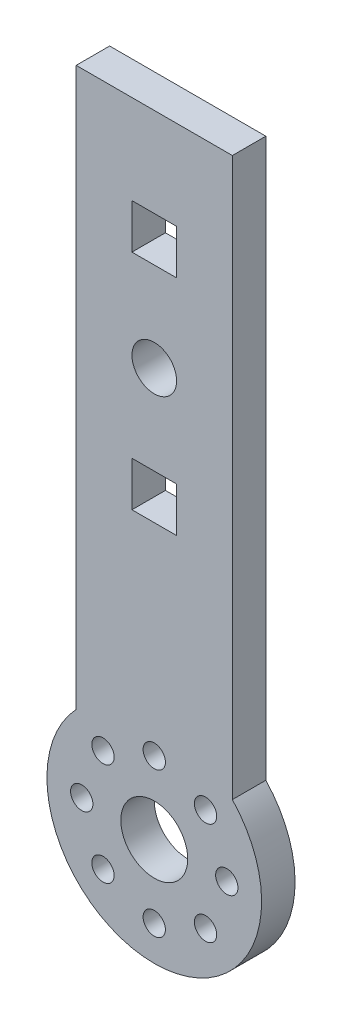
SolidWorks part; units mm, degrees
ref_plane "前视基准面" through (0, 0, 0) normal (0, 0, 1) x (1, 0, 0)
ref_plane "上视基准面" through (0, 0, 0) normal (0, 1, 0) x (1, 0, 0)
ref_plane "右视基准面" through (0, 0, 0) normal (1, 0, 0) x (0, 0, -1)
sketch "草图1" plane through (0, 0, 0) normal (0, 0, 1) x (1, 0, 0)
  line L1 (-7, -6.6001) -> (7, -6.6001)
  line L2 (-7, -6.6001) -> (-7, 6.6001)
  line L3 (-7, 6.6001) -> (7, 6.6001)
  line L4 (7, -6.6001) -> (7, 6.6001)
  line L5 (-7, -6.6001) -> (7, 6.6001) construction
  line L6 (-7, 6.6001) -> (7, -6.6001) construction
  line L7 (-7, 6.6001) -> (7, 6.6001)
  line L8 (-7, 6.6001) -> (-7, 56.6001)
  line L9 (-7, 56.6001) -> (7, 56.6001)
  line L10 (7, 6.6001) -> (7, 56.6001)
  circle A0 centre (0, 0) radius 9.6209
  dimension "D1" = 14
  dimension "D2" = 50
extrude "凸台-拉伸1" add sketch "草图1" along normal blind 3 contours A0 L10 L9 L8
sketch "草图3" plane through (0, 0, 3) normal (0, 0, 1) x (1, 0, 0)
  line L0 (0, 56.6001) -> (0, 46.6001)
  line L1 (-7, 56.6001) -> (7, 56.6001) construction
  line L2 (0, 46.6001) -> (0, 36.6001)
  line L3 (-2, 48.6001) -> (2, 48.6001)
  line L4 (-2, 48.6001) -> (-2, 44.6001)
  line L5 (-2, 44.6001) -> (2, 44.6001)
  line L6 (2, 48.6001) -> (2, 44.6001)
  line L7 (-2, 48.6001) -> (2, 44.6001) construction
  line L8 (-2, 44.6001) -> (2, 48.6001) construction
  line L9 (0, 36.6001) -> (0, 26.6001)
  line L10 (-2, 38.6001) -> (2, 38.6001)
  line L11 (-2, 38.6001) -> (-2, 34.6001)
  line L12 (-2, 34.6001) -> (2, 34.6001)
  line L13 (2, 38.6001) -> (2, 34.6001)
  line L14 (-2, 38.6001) -> (2, 34.6001) construction
  line L15 (-2, 34.6001) -> (2, 38.6001) construction
  line L17 (-2, 28.6001) -> (2, 28.6001)
  line L18 (-2, 28.6001) -> (-2, 24.6001)
  line L19 (-2, 24.6001) -> (2, 24.6001)
  line L20 (2, 28.6001) -> (2, 24.6001)
  line L21 (-2, 28.6001) -> (2, 24.6001) construction
  line L22 (-2, 24.6001) -> (2, 28.6001) construction
  dimension "D1" = 10
  dimension "D2" = 4
  dimension "D3" = 4
  dimension "D4" = 10
  dimension "D5" = 4
  dimension "D6" = 10
  dimension "D7" = 4
extrude "切除-拉伸2" cut sketch "草图3" against normal blind 3 flip side to cut
sketch "草图4" plane through (0, 0, 3) normal (0, 0, 1) x (1, 0, 0)
  circle A0 centre (0, 0) radius 3
extrude "切除-拉伸3" cut sketch "草图4" against normal blind 10
sketch "草图5" plane through (0, 0, 0) normal (0, 0, -1) x (-1, 0, 0)
  line L0 (0, 0) -> (0, 6.5)
  circle A0 centre (0, 6.5) radius 1
  dimension "D1" = 6.5
extrude "切除-拉伸4" cut sketch "草图5" against normal blind 10
sketch "草图6" plane through (0, 0, 0) normal (0, 0, -1) x (-1, 0, 0)
  line L1 (-2, 38.6001) -> (2, 38.6001)
  line L2 (-2, 38.6001) -> (-2, 34.6001)
  line L3 (-2, 34.6001) -> (2, 34.6001)
  line L4 (2, 38.6001) -> (2, 34.6001)
extrude "凸台-拉伸3" add sketch "草图6" against normal up to surface (3 mm away) up to face at (1, 6.5, 3)
sketch "草图7" plane through (0, 0, 0) normal (0, 0, -1) x (-1, 0, 0)
  line L0 (0, 28.6001) -> (0, 44.6001)
  line L1 (2, 28.6001) -> (-2, 28.6001) construction
  line L2 (2, 44.6001) -> (-2, 44.6001) construction
  circle A0 centre (0, 36.6001) radius 2
extrude "切除-拉伸5" cut sketch "草图7" against normal blind 10 contours L0 A0 | L0 A0
cosmetic thread "装饰螺纹线1" parameters "D2"=5
pattern_circular "阵列(圆周)1" count 8 over 360 about axis through (0, 0, 0) along (0, 0, 1) of "切除-拉伸4"
sketch "草图8" plane through (0, 0, 3) normal (0, 0, 1) x (1, 0, 0)
  line L0 (-2, 44.6001) -> (2, 44.6001) construction
  line L1 (2, 48.6001) -> (2, 44.6001) construction
  line L2 (-2, 48.6001) -> (2, 48.6001) construction
  line L3 (-7, 56.6001) -> (-7, 6.6001)
  line L4 (7, 6.6001) -> (7, 56.6001)
  line L5 (7, 56.6001) -> (-7, 56.6001)
  line L6 (-7, 56.6001) -> (-7, 6.6001)
  line L7 (7, 6.6001) -> (7, 56.6001)
  line L8 (7, 56.6001) -> (-7, 56.6001)
  line L9 (-2, 48.6001) -> (-2, 44.6001) construction
  line L10 (-2, 44.6001) -> (2, 44.6001)
  line L11 (2, 48.6001) -> (2, 44.6001)
  line L12 (-2, 48.6001) -> (2, 48.6001)
  line L13 (-2, 48.6001) -> (-2, 44.6001)
  line L14 (-2, 24.6001) -> (2, 24.6001) construction
  line L15 (2, 28.6001) -> (2, 24.6001) construction
  line L16 (-2, 28.6001) -> (2, 28.6001) construction
  line L17 (-2, 28.6001) -> (-2, 24.6001) construction
  line L18 (-2, 24.6001) -> (2, 24.6001)
  line L19 (2, 28.6001) -> (2, 24.6001)
  line L20 (-2, 28.6001) -> (2, 28.6001)
  line L21 (-2, 28.6001) -> (-2, 24.6001)
  circle A0 centre (0, 36.6001) radius 2 construction
  arc A1 (-7, 6.6001) -> (7, 6.6001) centre (0, 0) ccw
  arc A2 (-7, 6.6001) -> (7, 6.6001) centre (0, 0) ccw
  circle A3 centre (0, 36.6001) radius 2
  circle A4 centre (-4.5962, -4.5962) radius 1 construction
  circle A5 centre (-6.5, 0) radius 1 construction
  circle A6 centre (0, -6.5) radius 1 construction
  circle A7 centre (4.5962, -4.5962) radius 1 construction
  circle A8 centre (6.5, 0) radius 1 construction
  circle A9 centre (4.5962, 4.5962) radius 1 construction
  circle A10 centre (-4.5962, 4.5962) radius 1 construction
  circle A11 centre (0, 6.5) radius 1 construction
  circle A12 centre (0, 0) radius 3 construction
  circle A13 centre (-4.5962, -4.5962) radius 1
  circle A14 centre (-6.5, 0) radius 1
  circle A15 centre (0, -6.5) radius 1
  circle A16 centre (4.5962, -4.5962) radius 1
  circle A17 centre (6.5, 0) radius 1
  circle A18 centre (4.5962, 4.5962) radius 1
  circle A19 centre (-4.5962, 4.5962) radius 1
  circle A20 centre (0, 6.5) radius 1
  circle A21 centre (0, 0) radius 3
  dimension "D1" = 0
